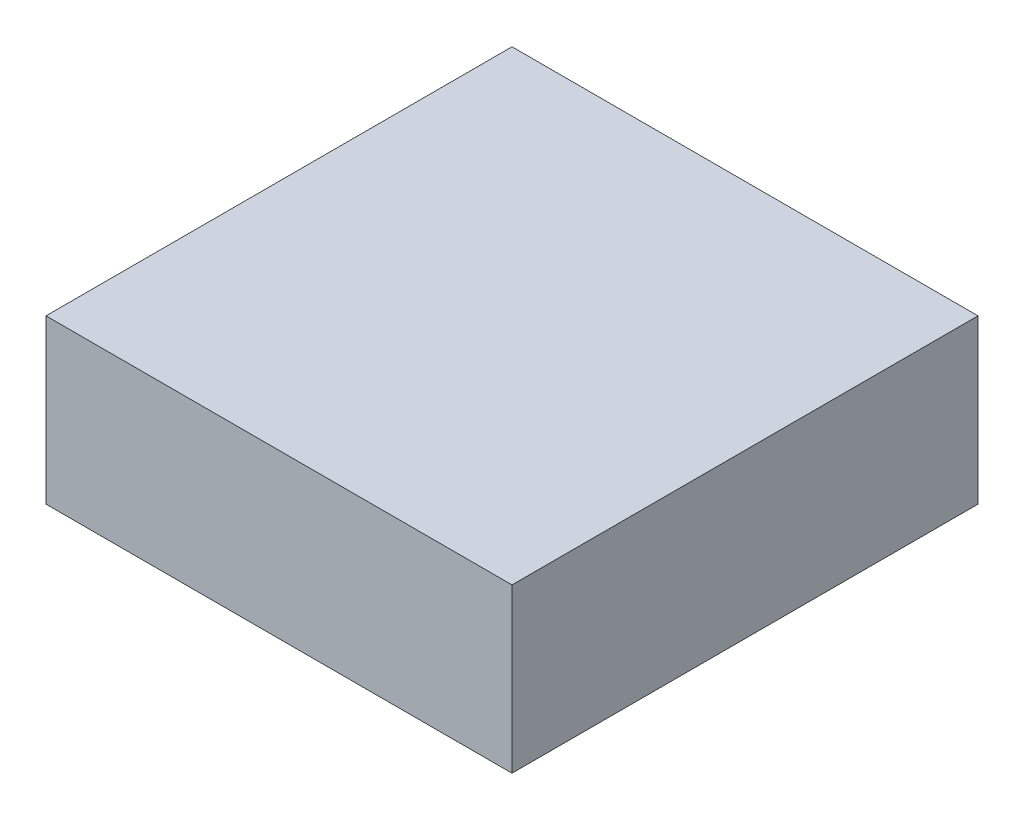
SolidWorks part; units mm, degrees
ref_plane "Front Plane" through (0, 0, 0) normal (0, 0, 1) x (1, 0, 0)
ref_plane "Top Plane" through (0, 0, 0) normal (0, 1, 0) x (1, 0, 0)
ref_plane "Right Plane" through (0, 0, 0) normal (1, 0, 0) x (0, 0, -1)
sketch "Sketch1" plane through (0, 0, 0) normal (0, 1, 0) x (1, 0, 0)
  line L1 (0, 0) -> (5, 0)
  line L2 (0, 0) -> (0, 5)
  line L3 (0, 5) -> (5, 5)
  line L4 (5, 0) -> (5, 5)
  dimension "D1" = 5
  dimension "D2" = 5
extrude "Boss-Extrude1" add sketch "Sketch1" along normal blind 1.75
